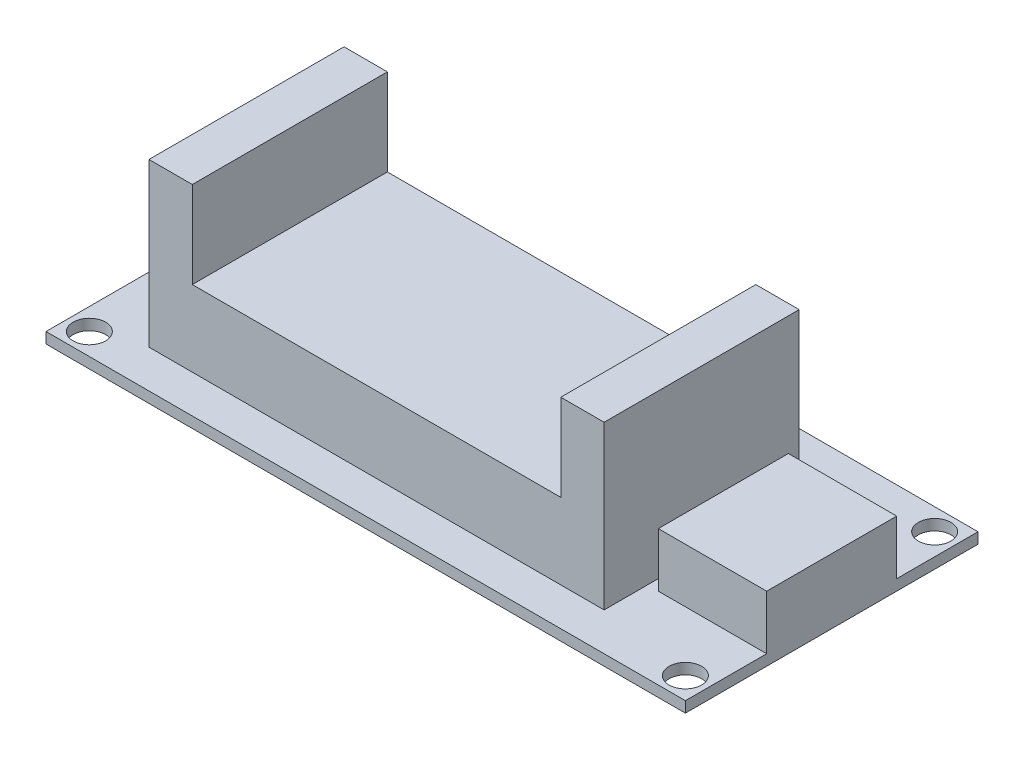
SolidWorks part; units mm, degrees
ref_plane "Front Plane" through (0, 0, 0) normal (0, 0, 1) x (1, 0, 0)
ref_plane "Top Plane" through (0, 0, 0) normal (0, 1, 0) x (1, 0, 0)
ref_plane "Right Plane" through (0, 0, 0) normal (1, 0, 0) x (0, 0, -1)
sketch "Sketch1" plane through (0, 0, 0) normal (0, 1, 0) x (1, 0, 0)
  line L0 (-26.1918, 19.3057) -> (28.8082, 19.3057) construction
  line L1 (-28.1918, 21.3057) -> (30.8082, 21.3057)
  line L2 (-28.1918, 21.3057) -> (-28.1918, -5.6943)
  line L3 (-28.1918, -5.6943) -> (30.8082, -5.6943)
  line L4 (30.8082, 21.3057) -> (30.8082, -5.6943)
  line L5 (28.8082, 19.3057) -> (28.8082, -3.6943) construction
  line L8 (28.8082, -3.6943) -> (-26.1918, -3.6943) construction
  line L9 (-26.1918, -3.6943) -> (-26.1918, 19.3057) construction
  circle A0 centre (-26.1918, -3.6943) radius 1.5
  circle A1 centre (-26.1918, 19.3057) radius 1.5
  circle A2 centre (28.8082, 19.3057) radius 1.5
  circle A3 centre (28.8082, -3.6943) radius 1.5
  dimension "D3" = 23
  dimension "D4" = 55
  dimension "D5" = 2
  dimension "D6" = 2
  dimension "D1" = 59
  dimension "D2" = 27
extrude "Boss-Extrude1" add sketch "Sketch1" along normal blind 1
sketch "Sketch2" plane through (0, 1, 0) normal (0, 1, 0) x (1, 0, 0)
  line L0 (-28.1918, 21.3057) -> (-28.1918, -5.6943) construction
  line L1 (-18.1918, 15.8057) -> (15.8082, 15.8057)
  line L2 (-18.1918, 15.8057) -> (-18.1918, -2.1943)
  line L3 (-18.1918, -2.1943) -> (15.8082, -2.1943)
  line L4 (15.8082, 15.8057) -> (15.8082, -2.1943)
  line L5 (30.8082, 21.3057) -> (-28.1918, 21.3057) construction
  dimension "D1" = 18
  dimension "D2" = 34
  dimension "D3" = 10
  dimension "D4" = 5.5
extrude "Boss-Extrude2" add sketch "Sketch2" along normal blind 7
sketch "Sketch3" plane through (0, 1, 0) normal (0, 1, 0) x (1, 0, 0)
  line L1 (-18.1918, 15.8057) -> (-22.1918, 15.8057)
  line L2 (-18.1918, 15.8057) -> (-18.1918, -2.1943)
  line L3 (-18.1918, -2.1943) -> (-22.1918, -2.1943)
  line L4 (-22.1918, 15.8057) -> (-22.1918, -2.1943)
  dimension "D1" = 4
extrude "Boss-Extrude3" add sketch "Sketch3" along normal blind 15
sketch "Sketch4" plane through (0, 1, 0) normal (0, 1, 0) x (1, 0, 0)
  line L1 (15.8082, 15.8057) -> (19.8082, 15.8057)
  line L2 (15.8082, 15.8057) -> (15.8082, -2.1943)
  line L3 (15.8082, -2.1943) -> (19.8082, -2.1943)
  line L4 (19.8082, 15.8057) -> (19.8082, -2.1943)
  dimension "D1" = 4
extrude "Boss-Extrude4" add sketch "Sketch4" along normal blind 15
sketch "Sketch7" plane through (0, 1, 0) normal (0, 1, 0) x (1, 0, 0)
  line L0 (30.8082, -5.6943) -> (30.8082, 21.3057) construction
  line L1 (20.8082, 13.8057) -> (30.8082, 13.8057)
  line L2 (20.8082, 13.8057) -> (20.8082, 1.8057)
  line L3 (20.8082, 1.8057) -> (30.8082, 1.8057)
  line L4 (30.8082, 13.8057) -> (30.8082, 1.8057)
  line L5 (-28.1918, -5.6943) -> (30.8082, -5.6943) construction
  dimension "D1" = 10
  dimension "D2" = 12
  dimension "D3" = 7.5
extrude "Boss-Extrude7" add sketch "Sketch7" along normal blind 5
sketch "Sketch8" plane through (0, 1, 0) normal (0, 1, 0) x (1, 0, 0)
  line L0 (-28.1918, 21.3057) -> (-28.1918, -5.6943) construction
  line L1 (-28.1918, 11.2307) -> (-22.1918, 11.2307)
  line L2 (-28.1918, 11.2307) -> (-28.1918, 4.3807)
  line L3 (-28.1918, 4.3807) -> (-22.1918, 4.3807)
  line L4 (-22.1918, 11.2307) -> (-22.1918, 4.3807)
  line L5 (-22.1918, 15.8057) -> (-22.1918, -2.1943) construction
  line L6 (-28.1918, -5.6943) -> (30.8082, -5.6943) construction
  dimension "D1" = 6.85
  dimension "D2" = 10.075
extrude "Boss-Extrude8" add sketch "Sketch8" along normal blind 1.8
